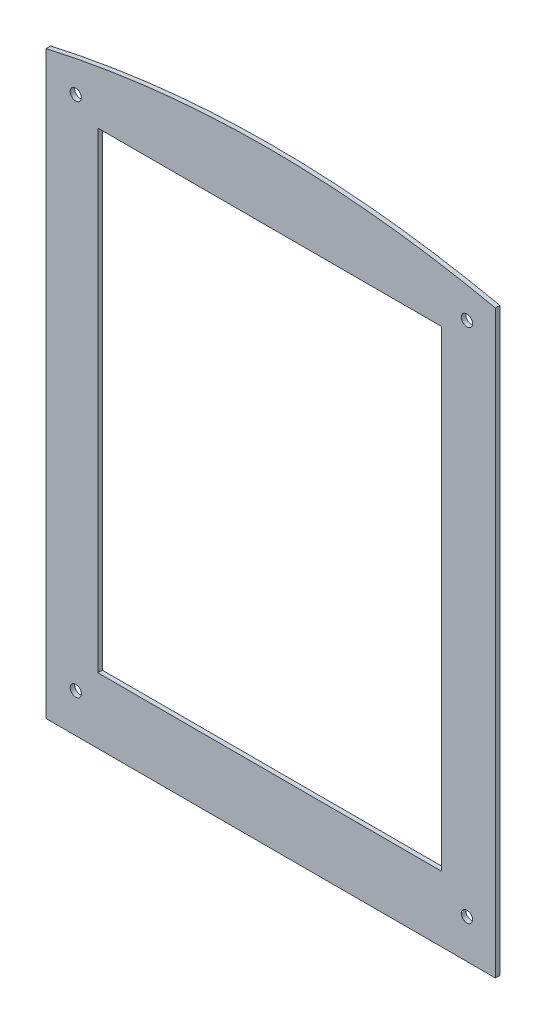
SolidWorks part; units mm, degrees
ref_plane "Front Plane" through (0, 0, 0) normal (0, 0, 1) x (1, 0, 0)
ref_plane "Top Plane" through (0, 0, 0) normal (0, 1, 0) x (1, 0, 0)
ref_plane "Right Plane" through (0, 0, 0) normal (1, 0, 0) x (0, 0, -1)
sketch "Sketch1" plane through (0, 0, 0) normal (0, 0, 1) x (1, 0, 0)
  line L0 (79.9897, 0) -> (-120.0103, 0)
  line L1 (-120.0103, 0) -> (-120.0103, 258.3)
  line L3 (79.9897, 258.3) -> (79.9897, 0)
  line L7 (55.9971, 239.1788) -> (-97.0029, 239.1788)
  line L10 (55.9971, 239.1788) -> (55.9971, 29.1788)
  line L13 (55.9971, 29.1788) -> (-97.0029, 29.1788)
  line L16 (-97.0029, 239.1788) -> (-97.0029, 29.1788)
  circle A22 centre (-106.8037, 247.1774) radius 2.5
  circle A23 centre (67.3225, 247.1774) radius 2.5
  circle A24 centre (67.3225, 17.3422) radius 2.5
  circle A25 centre (-106.8037, 17.3422) radius 2.5
  spline S0 degree 2 poles (-120.0103, 258.3) (-22.4945, 280.451) (79.9897, 258.3) knots 0 0 0 1 1 1
  dimension "D4" = 210
  dimension "D1" = 258.3
  dimension "D2" = 200
  dimension "D3" = 153
extrude "Boss-Extrude1" add sketch "Sketch1" along normal blind 2
